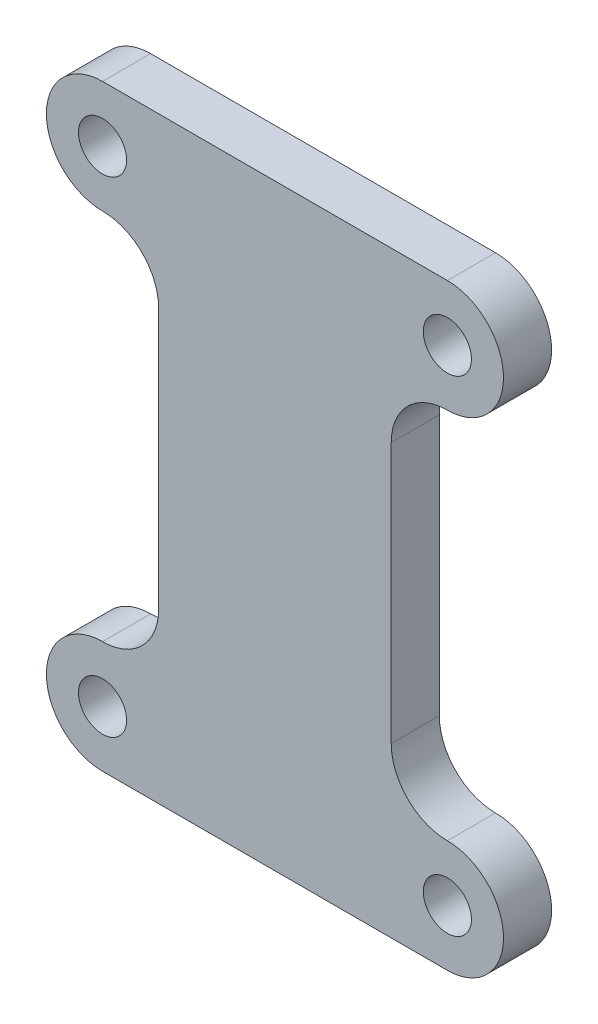
SolidWorks part; units mm, degrees
material "3D_printed_PLA"
ref_plane "Front Plane" through (0, 0, 0) normal (0, 0, 1) x (1, 0, 0)
ref_plane "Top Plane" through (0, 0, 0) normal (0, 1, 0) x (1, 0, 0)
ref_plane "Right Plane" through (0, 0, 0) normal (1, 0, 0) x (0, 0, -1)
sketch "Sketch1" plane through (0, 0, 0) normal (0, 0, 1) x (1, 0, 0)
  line L0 (-10.75, 18.625) -> (10.75, 18.625)
  line L1 (10.75, -15.125) -> (-10.75, -15.125) construction
  line L2 (10.75, -15.125) -> (10.75, 15.125) construction
  line L3 (10.75, 15.125) -> (-10.75, 15.125) construction
  line L4 (-10.75, -15.125) -> (-10.75, 15.125) construction
  line L5 (10.75, -15.125) -> (-10.75, 15.125) construction
  line L6 (10.75, 15.125) -> (-10.75, -15.125) construction
  line L7 (7.25, 8.125) -> (7.25, -8.125)
  line L8 (7.25, 0) -> (0, 0) construction
  line L9 (-7.25, 8.125) -> (-7.25, -8.125)
  line L10 (-10.75, -18.625) -> (10.75, -18.625)
  arc A0 (-10.75, 11.625) -> (-10.75, 18.625) centre (-10.75, 15.125) cw
  arc A1 (10.75, 18.625) -> (10.75, 11.625) centre (10.75, 15.125) cw
  arc A2 (10.75, 11.625) -> (7.25, 8.125) centre (10.75, 8.125) ccw
  arc A3 (-10.75, 11.625) -> (-7.25, 8.125) centre (-10.75, 8.125) cw
  arc A4 (-10.75, -11.625) -> (-7.25, -8.125) centre (-10.75, -8.125) ccw
  arc A5 (10.75, -11.625) -> (7.25, -8.125) centre (10.75, -8.125) cw
  arc A6 (10.75, -18.625) -> (10.75, -11.625) centre (10.75, -15.125) ccw
  arc A7 (-10.75, -11.625) -> (-10.75, -18.625) centre (-10.75, -15.125) ccw
  circle A8 centre (-10.75, 15.125) radius 1.5
  circle A9 centre (10.75, 15.125) radius 1.5
  circle A10 centre (10.75, -15.125) radius 1.5
  circle A11 centre (-10.75, -15.125) radius 1.5
  point P0 (0, 0)
  point P30 (-7.25, 0)
  dimension "D3" = 3.5
  dimension "D4" = 3
  dimension "D1" = 30.25
  dimension "D2" = 21.5
extrude "Boss-Extrude1" add sketch "Sketch1" along normal mid plane 3
